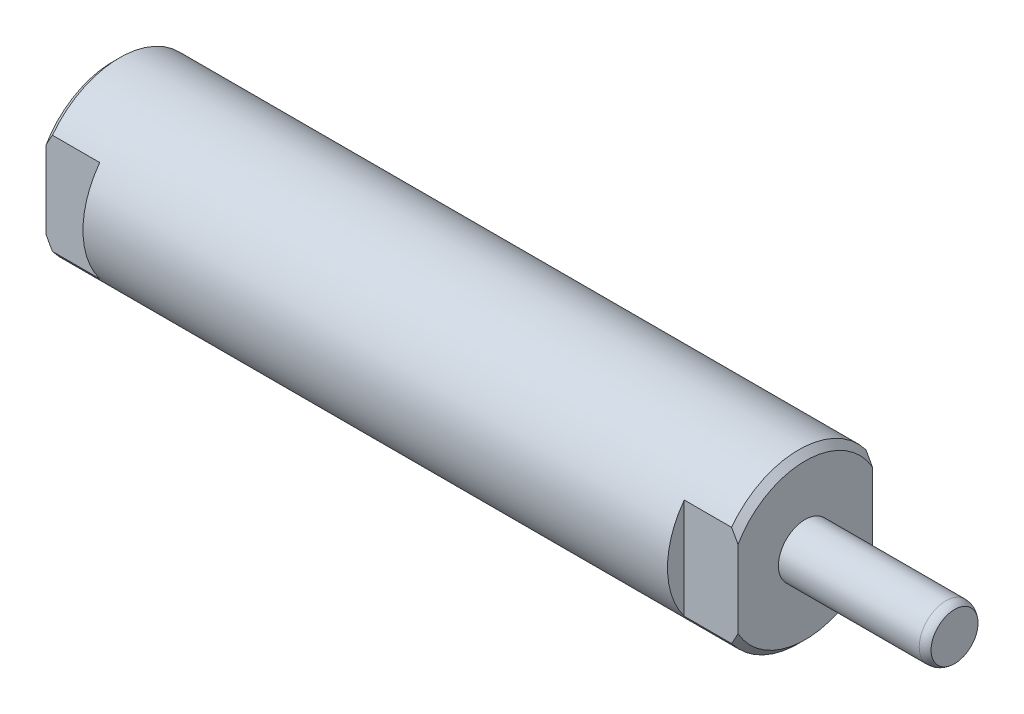
SolidWorks part; units mm, degrees
material "Alloy Steel"
ref_plane "Front Plane" through (0, 0, 0) normal (0, 0, 1) x (1, 0, 0)
ref_plane "Top Plane" through (0, 0, 0) normal (0, 1, 0) x (1, 0, 0)
ref_plane "Right Plane" through (0, 0, 0) normal (1, 0, 0) x (0, 0, -1)
ref_plane "Plane1" through (0, 0, 0) normal (0, 0, -1) x (-1, 0, 0)
sketch "Sketch1" plane through (0, 0, 0) normal (0, 0, -1) x (-1, 0, 0)
  line L0 (-99.4156, 2.7742) -> (-99.4156, 0)
  line L1 (-99.4156, 0) -> (0, 0)
  line L2 (0, 0) -> (0, 9.9185)
  line L4 (0, 9.9185) -> (-81.7626, 9.9185)
  line L6 (-81.7626, 9.9185) -> (-81.7626, 3.1623)
  line L7 (-81.7626, 3.1623) -> (-98.3996, 3.1623)
  line L8 (-99.4156, 0) -> (0, 0) construction
  line L9 (0, 0) -> (6.3339, 0) construction
  arc A0 (-98.3996, 3.1623) -> (-99.4156, 2.7742) centre (-98.3996, 1.6383) ccw
  dimension "D6" = 1.524
  dimension "D1" = 19.837
  dimension "D4" = 6.3246
  dimension "D5" = 1.016
  dimension "D7" = 17.653
  dimension "D8" = 81.7626
revolve "Revolve1" add sketch "Sketch1" angle 360 about L8
sketch "Sketch2" plane through (0, 0, 0) normal (0, 0, -1) x (-1, 0, 0)
  line L0 (0, 0) -> (-25.1118, 0) construction
  line L1 (0, 0) -> (0, 4.953)
  line L2 (0, -9.9185) -> (0, 9.9185) construction
  line L3 (0, 4.953) -> (-0.127, 4.953)
  line L4 (-0.127, 4.953) -> (-0.6604, 4.4196)
  line L5 (-0.6604, 4.4196) -> (-10.5664, 4.4196)
  line L6 (-10.5664, 4.4196) -> (-10.5664, 0)
  line L7 (-10.5664, 0) -> (0, 0)
  dimension "D1" = 9.906
  dimension "D2" = 10.5664
  dimension "D3" = 45
  dimension "D4" = 0.127
  dimension "D5" = 8.8392
revolve "Cut-Revolve1" cut sketch "Sketch2" angle 360 about L0
chamfer "Chamfer1" distance 0.762 angle 45 2 edges at (0, 0, 9.9185) (81.7626, 0, 9.9185)
sketch "Sketch5" plane through (0, 0, 0) normal (0, 1, 0) x (1, 0, 0)
  line L0 (0, 0) -> (18.2862, 0) construction
  line L1 (0, 7.9375) -> (6.35, 7.9375)
  line L2 (6.35, 7.9375) -> (6.35, 9.9185)
  line L3 (81.0006, 9.9185) -> (0.762, 9.9185) construction
  line L4 (6.35, 9.9185) -> (0, 9.9185)
  line L5 (0, 9.9185) -> (0, 7.9375)
  line L6 (0, 9.1565) -> (0, -9.1565) construction
  line L7 (0, -9.9185) -> (0, -7.9375)
  line L8 (6.35, -9.9185) -> (0, -9.9185)
  line L9 (6.35, -7.9375) -> (6.35, -9.9185)
  line L10 (0, -7.9375) -> (6.35, -7.9375)
  dimension "D1" = 90
  dimension "D2" = 6.35
  dimension "D3" = 15.875
extrude "Cut-Extrude1" cut sketch "Sketch5" against normal through all and the other way through all
sketch "Sketch6" plane through (0, 0, 0) normal (0, 1, 0) x (1, 0, 0)
  line L0 (81.7626, -9.1565) -> (81.7626, 9.1565) construction
  line L1 (81.7626, 7.9375) -> (75.4126, 7.9375)
  line L2 (81.7626, 7.9375) -> (81.7626, 9.9185)
  line L3 (81.7626, 9.9185) -> (75.4126, 9.9185)
  line L4 (75.4126, 7.9375) -> (75.4126, 9.9185)
  line L5 (81.0006, 9.9185) -> (6.35, 9.9185) construction
  line L6 (6.35, -9.9185) -> (81.0006, -9.9185) construction
  line L7 (81.7626, -7.9375) -> (75.4126, -7.9375)
  line L8 (81.7626, -7.9375) -> (81.7626, -9.9185)
  line L9 (81.7626, -9.9185) -> (75.4126, -9.9185)
  line L10 (75.4126, -7.9375) -> (75.4126, -9.9185)
  dimension "D1" = 6.35
  dimension "D2" = 15.875
extrude "Cut-Extrude2" cut sketch "Sketch6" against normal through all and the other way through all
